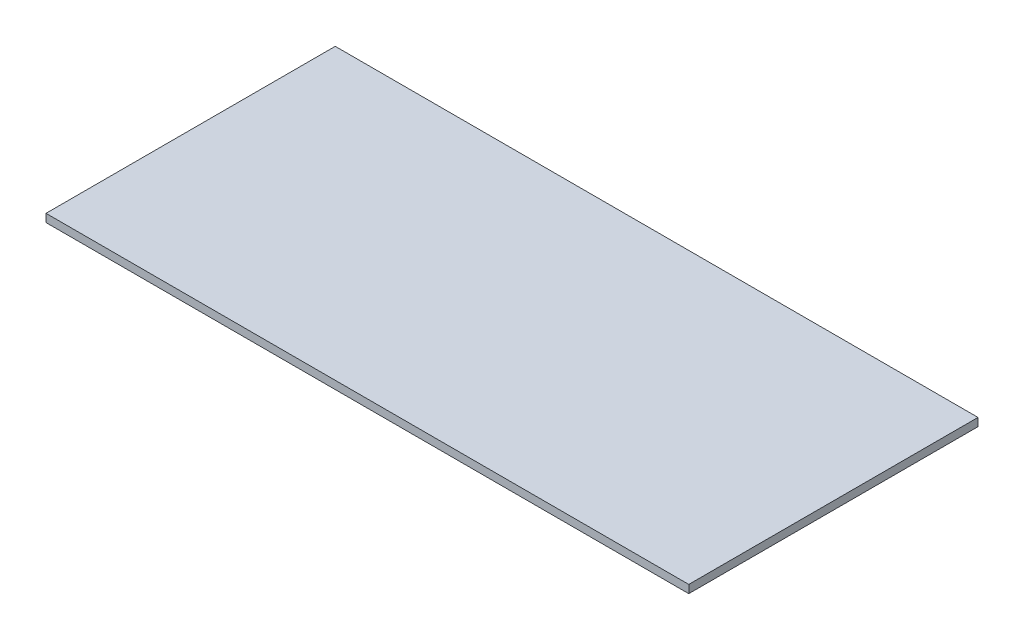
SolidWorks part; units mm, degrees
ref_plane "Спереди" through (0, 0, 0) normal (0, 0, 1) x (1, 0, 0)
ref_plane "Сверху" through (0, 0, 0) normal (0, 1, 0) x (1, 0, 0)
ref_plane "Справа" through (0, 0, 0) normal (1, 0, 0) x (0, 0, -1)
sketch "Эскиз1" plane through (0, 0, 0) normal (0, 1, 0) x (1, 0, 0)
  line L1 (-400, 180) -> (400, 180)
  line L2 (-400, 180) -> (-400, -180)
  line L3 (-400, -180) -> (400, -180)
  line L4 (400, 180) -> (400, -180)
  line L5 (-400, 180) -> (400, -180) construction
  line L6 (-400, -180) -> (400, 180) construction
  point P0 (0, 0)
  dimension "D1" = 800
extrude "Бобышка-Вытянуть1" add sketch "Эскиз1" along normal blind 10
